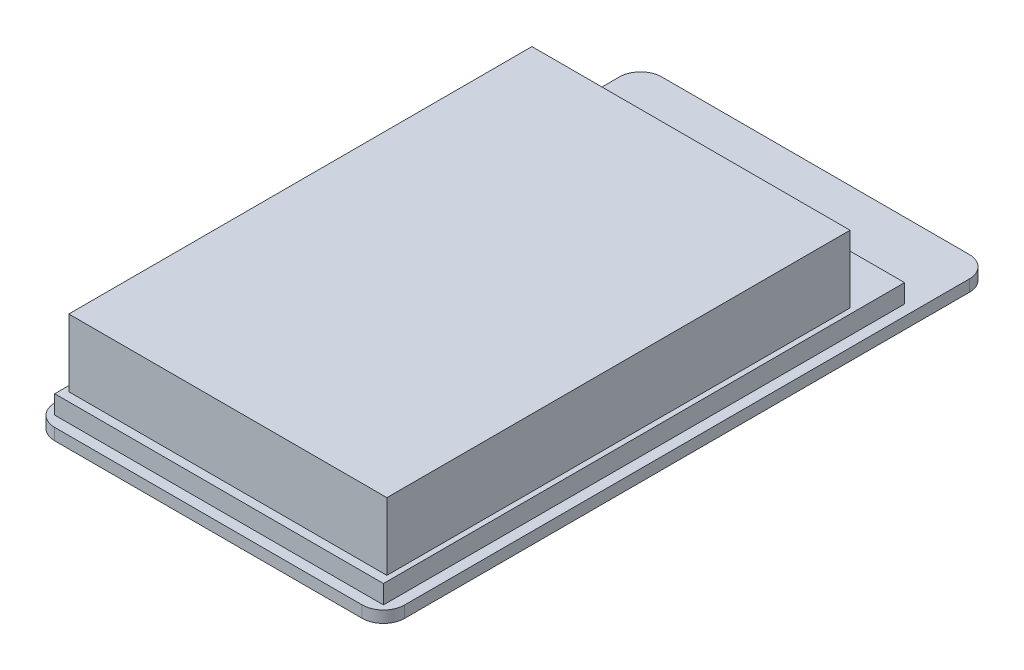
SolidWorks part; units mm, degrees
ref_plane "Front Plane" through (0, 0, 0) normal (0, 0, 1) x (1, 0, 0)
ref_plane "Top Plane" through (0, 0, 0) normal (0, 1, 0) x (1, 0, 0)
ref_plane "Right Plane" through (0, 0, 0) normal (1, 0, 0) x (0, 0, -1)
sketch "스케치1" plane through (0, 0, 0) normal (0, 1, 0) x (1, 0, 0)
  line L0 (0, 0) -> (0, 50000) construction
  line L1 (-33, 57.25) -> (33, 57.25)
  line L2 (-33, 57.25) -> (-33, -57.25)
  line L3 (-33, -57.25) -> (33, -57.25)
  line L4 (33, 57.25) -> (33, -57.25)
  line L5 (0, 0) -> (50000, 0) construction
  dimension "D1" = 66
  dimension "D2" = 33
  dimension "D3" = 114.5
  dimension "D4" = 57.25
extrude "보스-돌출1" add sketch "스케치1" along normal blind 2.2
fillet "필렛1" radius 4 4 edges at (33, 1.1, -57.25) (-33, 1.1, -57.25) (-33, 1.1, 57.25) (33, 1.1, 57.25)
sketch "스케치2" plane through (0, 2.2, 0) normal (0, 1, 0) x (1, 0, 0)
  line L0 (0, 0) -> (0, 50000) construction
  line L1 (-31, 43.05) -> (31, 43.05)
  line L2 (-31, 43.05) -> (-31, -55.25)
  line L3 (-31, -55.25) -> (31, -55.25)
  line L4 (31, 43.05) -> (31, -55.25)
  line L5 (0, 0) -> (50000, 0) construction
  line L6 (-29, -57.25) -> (29, -57.25) construction
  dimension "D1" = 62
  dimension "D2" = 31
  dimension "D3" = 2
  dimension "D4" = 98.3
extrude "보스-돌출2" add sketch "스케치2" along normal blind 3.5
sketch "스케치3" plane through (0, 5.7, 0) normal (0, 1, 0) x (1, 0, 0)
  line L0 (0, 0) -> (0, -50000) construction
  line L1 (-31, -55.25) -> (31, -55.25) construction
  line L2 (-30, 33.7647) -> (30, 33.7647)
  line L3 (-30, 33.7647) -> (-30, -53.6)
  line L4 (-30, -53.6) -> (30, -53.6)
  line L5 (30, 33.7647) -> (30, -53.6)
  dimension "D1" = 1.65
  dimension "D2" = 60
  dimension "D3" = 30
extrude "보스-돌출3" add sketch "스케치3" along normal blind 12.7
